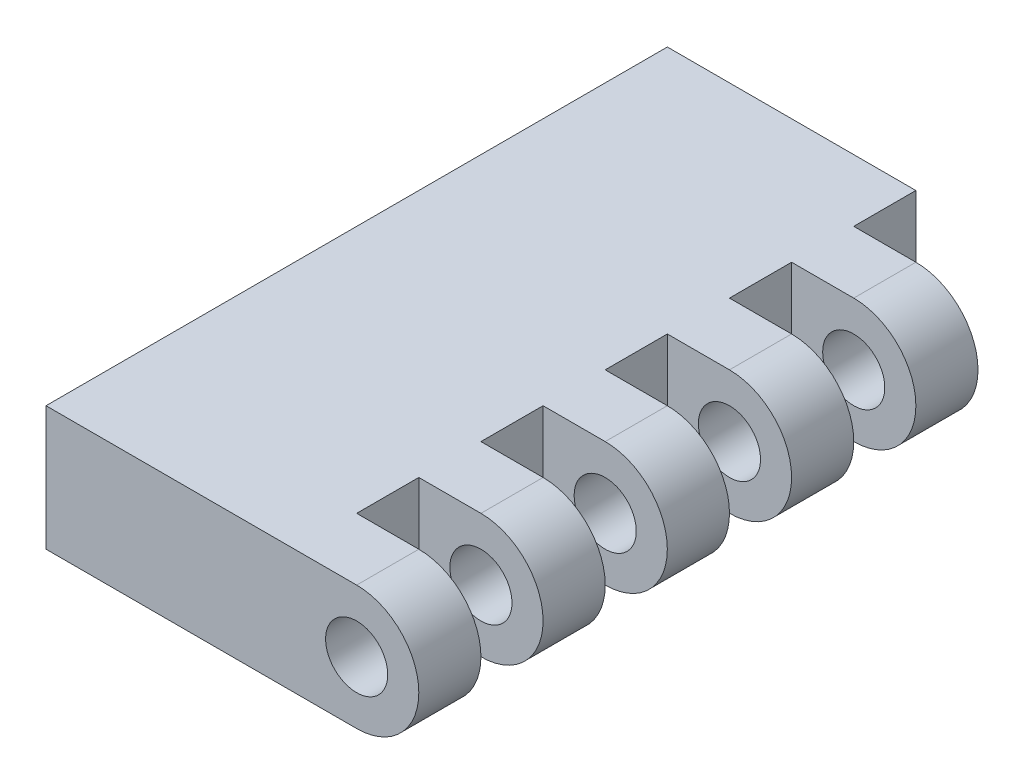
SolidWorks part; units mm, degrees
ref_plane "Front Plane" through (0, 0, 0) normal (0, 0, 1) x (1, 0, 0)
ref_plane "Top Plane" through (0, 0, 0) normal (0, 1, 0) x (1, 0, 0)
ref_plane "Right Plane" through (0, 0, 0) normal (1, 0, 0) x (0, 0, -1)
sketch "Sketch1" plane through (0, 0, 0) normal (0, 0, 1) x (1, 0, 0)
  line L0 (0, 0.254) -> (-1.27, 0.254)
  line L1 (-1.27, 0.254) -> (-1.27, -0.254)
  line L2 (-1.27, -0.254) -> (0, -0.254)
  arc A0 (0, -0.254) -> (0, 0.254) centre (0, 0) ccw
  circle A1 centre (0, 0) radius 0.127
  dimension "D1" = 0.508
  dimension "D3" = 0.254
  dimension "D4" = 0.254
  dimension "D2" = 1.27
extrude "Boss-Extrude1" add sketch "Sketch1" along normal blind 2.54
sketch "Sketch2" plane through (0, 0.254, 0) normal (0, 1, 0) x (1, 0, 0)
  line L0 (0, 0) -> (-1.27, 0) construction
  line L1 (-0.254, 0) -> (0.254, 0)
  line L2 (-0.254, 0) -> (-0.254, -0.254)
  line L3 (-0.254, -0.254) -> (0.254, -0.254)
  line L4 (0.254, 0) -> (0.254, -0.254)
  line L5 (0.254, -2.54) -> (0.254, 0) construction
  line L6 (-0.254, -0.508) -> (0.254, -0.508)
  line L7 (-0.254, -0.508) -> (-0.254, -0.762)
  line L8 (-0.254, -0.762) -> (0.254, -0.762)
  line L9 (0.254, -0.508) -> (0.254, -0.762)
  line L10 (-0.254, -1.016) -> (0.254, -1.016)
  line L11 (-0.254, -1.016) -> (-0.254, -1.27)
  line L12 (-0.254, -1.27) -> (0.254, -1.27)
  line L13 (0.254, -1.016) -> (0.254, -1.27)
  line L14 (-0.254, -1.524) -> (0.254, -1.524)
  line L15 (-0.254, -1.524) -> (-0.254, -1.778)
  line L16 (-0.254, -1.778) -> (0.254, -1.778)
  line L17 (0.254, -1.524) -> (0.254, -1.778)
  line L18 (-0.254, -2.032) -> (0.254, -2.032)
  line L19 (-0.254, -2.032) -> (-0.254, -2.286)
  line L20 (-0.254, -2.286) -> (0.254, -2.286)
  line L21 (0.254, -2.032) -> (0.254, -2.286)
  dimension "D1" = 0.508
  dimension "D2" = 0.254
  dimension "D3" = 5
extrude "Cut-Extrude1" cut sketch "Sketch2" against normal through all
